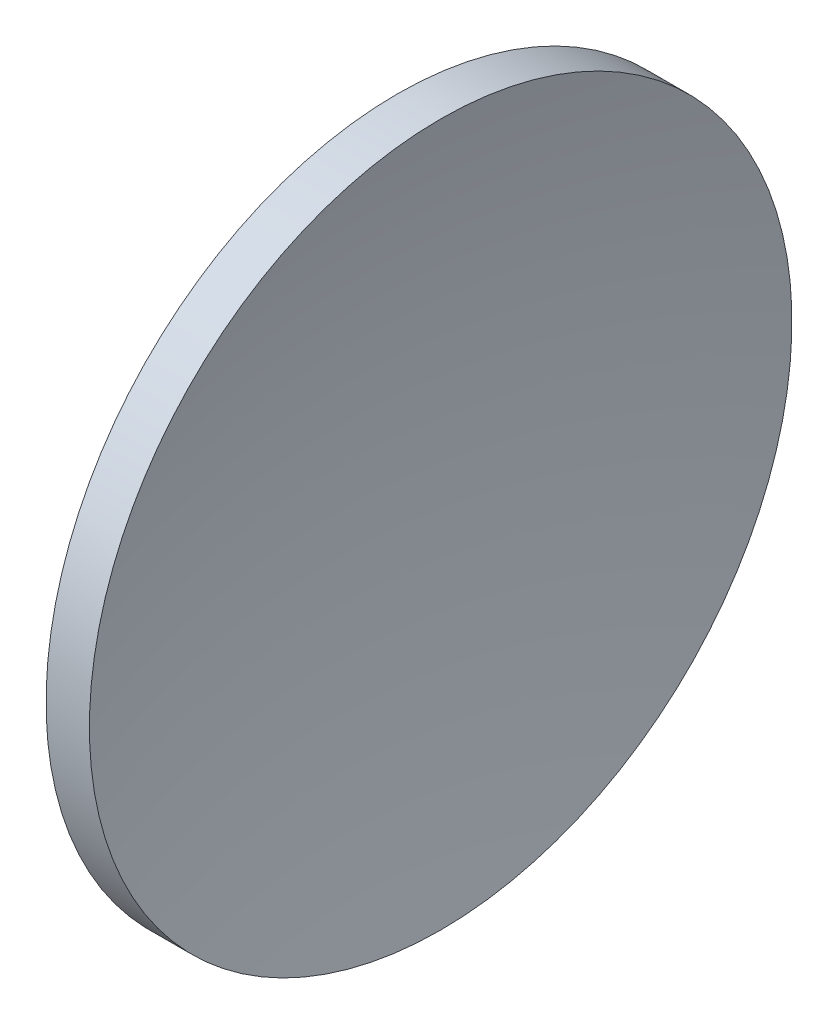
SolidWorks part; units mm, degrees
ref_plane "前视基准面" through (0, 0, 0) normal (0, 0, 1) x (1, 0, 0)
ref_plane "上视基准面" through (0, 0, 0) normal (0, 1, 0) x (1, 0, 0)
ref_plane "右视基准面" through (0, 0, 0) normal (1, 0, 0) x (0, 0, -1)
sketch "草图1" plane through (0, 0, 0) normal (0, 0, 1) x (1, 0, 0)
  line L0 (115.9445, 65.2168) -> (135.9482, 65.2168) construction
  line L1 (128.7605, 84.2418) -> (131.1071, 84.2418)
  line L2 (122.8554, 65.2168) -> (128.8554, 65.2168)
  arc A0 (128.7605, 84.2418) -> (122.8554, 65.2168) centre (156.4554, 65.2168) ccw
  arc A1 (131.1071, 84.2418) -> (128.8554, 65.2168) centre (210.3554, 65.2168) ccw
revolve "旋转1" add sketch "草图1" angle 360 about L0
